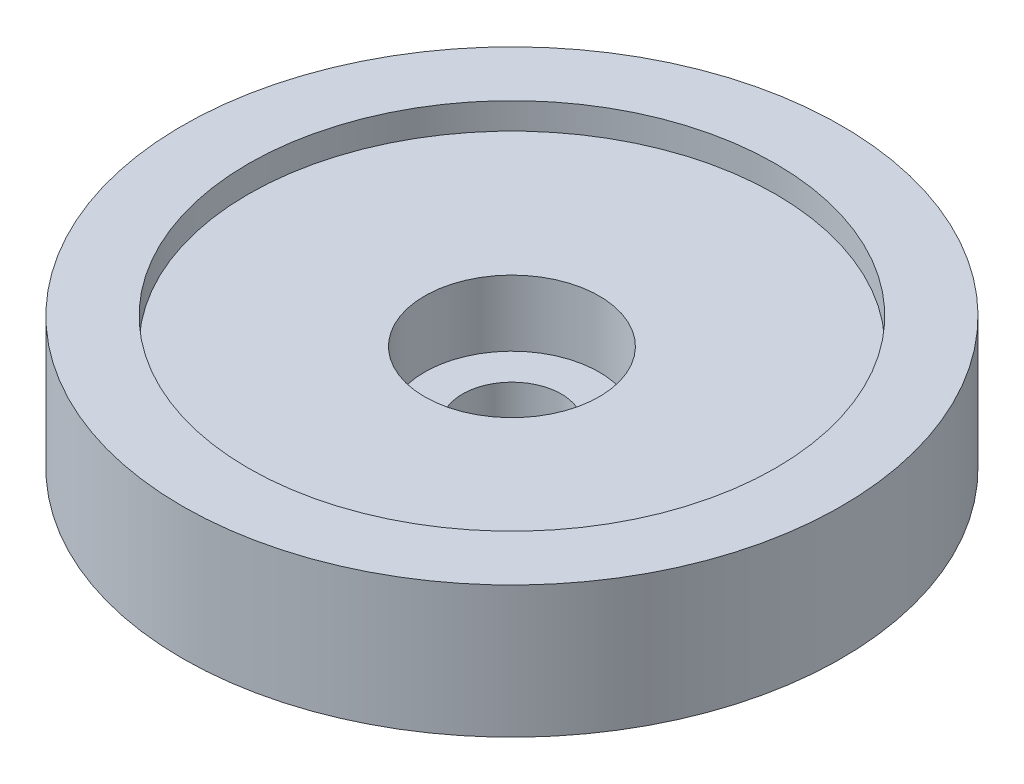
SolidWorks part; units mm, degrees
ref_plane "Front Plane" through (0, 0, 0) normal (0, 0, 1) x (1, 0, 0)
ref_plane "Top Plane" through (0, 0, 0) normal (0, 1, 0) x (1, 0, 0)
ref_plane "Right Plane" through (0, 0, 0) normal (1, 0, 0) x (0, 0, -1)
sketch "Sketch1" plane through (0, 0, 0) normal (0, 1, 0) x (1, 0, 0)
  line L0 (-391.1409, 0) -> (19165.9026, 0) construction
  line L1 (0, -391.1409) -> (0, 19165.9026) construction
  circle A0 centre (0, 0) radius 25
  dimension "D1" = 50
extrude "Boss-Extrude1" add sketch "Sketch1" along normal blind 10
sketch "Sketch2" plane through (0, 10, 0) normal (0, 1, 0) x (1, 0, 0)
  circle A0 centre (0, 0) radius 20
  dimension "D1" = 40
extrude "Cut-Extrude1" cut sketch "Sketch2" against normal blind 2
sketch "Sketch3" plane through (0, 8, 0) normal (0, 1, 0) x (1, 0, 0)
  circle A0 centre (0, 0) radius 6.625
  dimension "D1" = 13.25
extrude "Cut-Extrude2" cut sketch "Sketch3" against normal blind 5
sketch "Sketch4" plane through (0, 3, 0) normal (0, 1, 0) x (1, 0, 0)
  circle A0 centre (0, 0) radius 3.75
  dimension "D1" = 7.5
extrude "Cut-Extrude4" cut sketch "Sketch4" against normal through all both and the other way through all
